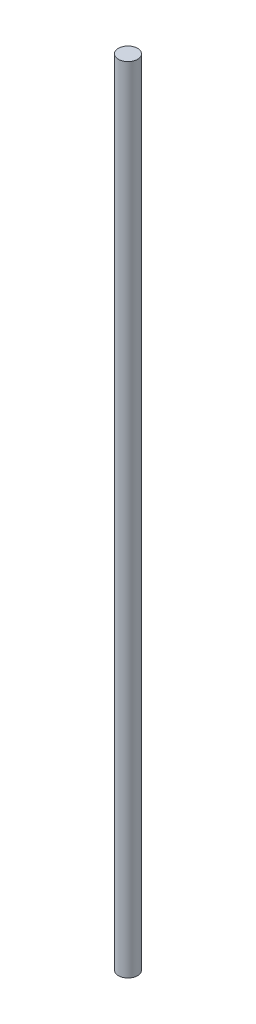
SolidWorks part; units mm, degrees
ref_plane "Front Plane" through (0, 0, 0) normal (0, 0, 1) x (1, 0, 0)
ref_plane "Top Plane" through (0, 0, 0) normal (0, 1, 0) x (1, 0, 0)
ref_plane "Right Plane" through (0, 0, 0) normal (1, 0, 0) x (0, 0, -1)
sketch "Sketch2" plane through (0, 0, 0) normal (0, 1, 0) x (1, 0, 0)
  circle A0 centre (0, 0) radius 3.4
  dimension "D1" = 6.8
extrude "Boss-Extrude1" add sketch "Sketch2" along normal blind 282
